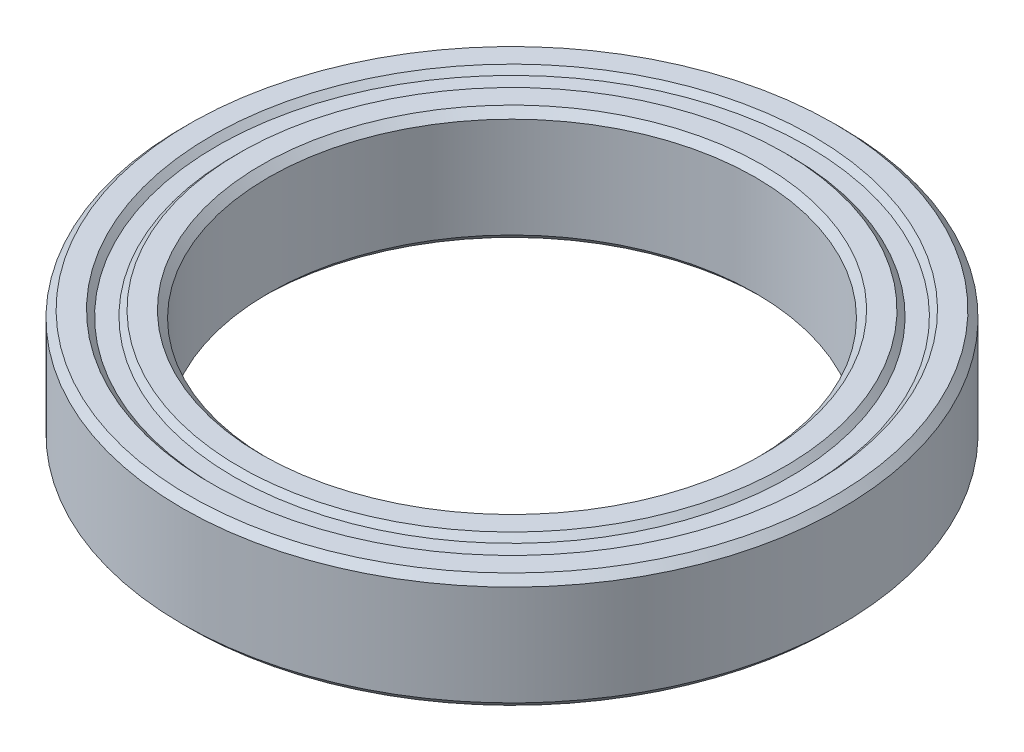
SolidWorks part; units mm, degrees
material "Stainless Steel (ferritic)"
ref_plane "Front Plane" through (0, 0, 0) normal (0, 0, 1) x (1, 0, 0)
ref_plane "Top Plane" through (0, 0, 0) normal (0, 1, 0) x (1, 0, 0)
ref_plane "Right Plane" through (0, 0, 0) normal (1, 0, 0) x (0, 0, -1)
sketch "Sketch1" plane through (0, 0, 0) normal (0, 0, 1) x (1, 0, 0)
  line L0 (0, -1.3494) -> (0, 70.5256) construction
  line L1 (8.5, 1.75) -> (8.5, -1.75)
  line L2 (8.5, -1.75) -> (8.75, -2)
  line L3 (8.75, -2) -> (9.5, -2)
  line L4 (9.5, -2) -> (9.7, -1.8)
  line L5 (9.7, -1.8) -> (10.3, -1.8)
  line L6 (10.3, -1.8) -> (10.5, -2)
  line L7 (10.5, -2) -> (11.25, -2)
  line L8 (11.25, -2) -> (11.5, -1.75)
  line L9 (11.5, -1.75) -> (11.5, 1.75)
  line L10 (11.5, 1.75) -> (11.25, 2)
  line L11 (11.25, 2) -> (10.5, 2)
  line L12 (10.5, 2) -> (10.3, 1.8)
  line L13 (10.3, 1.8) -> (9.7, 1.8)
  line L14 (9.7, 1.8) -> (9.5, 2)
  line L15 (9.5, 2) -> (8.75, 2)
  line L16 (8.75, 2) -> (8.5, 1.75)
  line L17 (0, 0) -> (8.5, 0) construction
  dimension "D1" = 8.5
  dimension "D2" = 4
  dimension "D3" = 0.25
  dimension "D4" = 0.2
  dimension "D5" = 11.5
  dimension "D6" = 0.75
revolve "Revolve1" add sketch "Sketch1" angle 360 about L0
